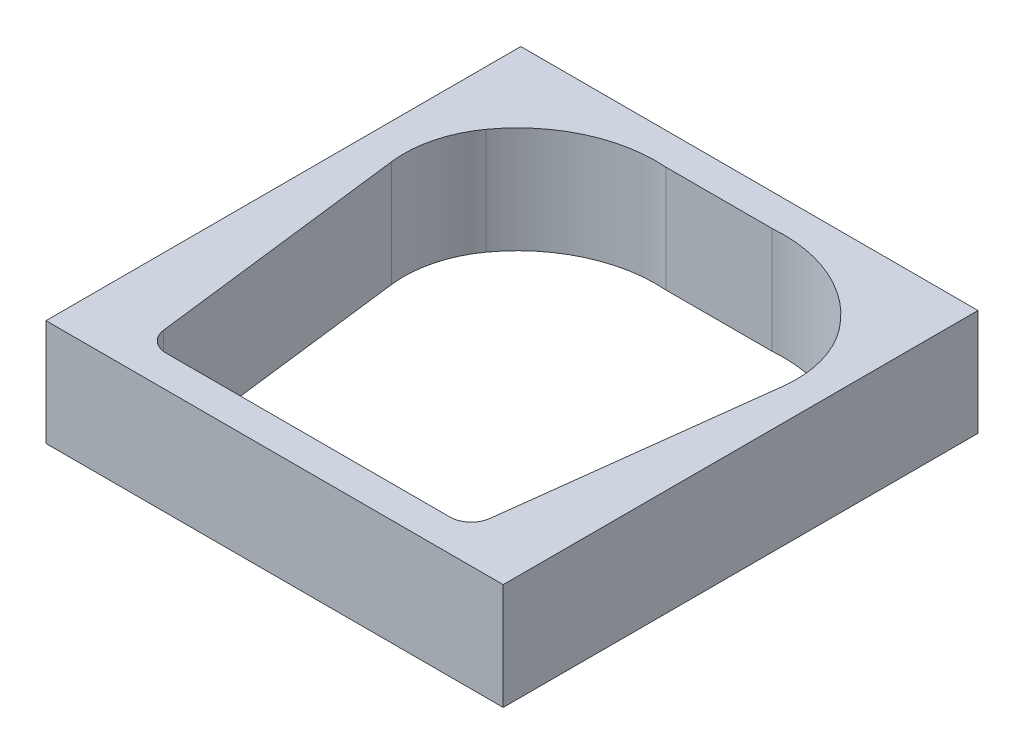
SolidWorks part; units mm, degrees
ref_plane "Front Plane" through (0, 0, 0) normal (0, 0, 1) x (1, 0, 0)
ref_plane "Top Plane" through (0, 0, 0) normal (0, 1, 0) x (1, 0, 0)
ref_plane "Right Plane" through (0, 0, 0) normal (1, 0, 0) x (0, 0, -1)
sketch "Sketch1" plane through (0, 0, 0) normal (0, 1, 0) x (1, 0, 0)
  line L1 (13.6302, 10) -> (23.6302, 10)
  line L3 (0.2982, -2.4286) -> (3.2992, -26.87)
  line L4 (5.2843, -28.6263) -> (31.976, -28.6263)
  line L5 (36.9706, -2.3598) -> (33.9611, -26.87)
  arc A0 (2.1102, 4.6358) -> (13.6302, 10) centre (12.6577, -2.9636) cw
  arc A1 (34.9994, 4.9193) -> (23.6302, 10) centre (24.6588, -2.9592) ccw
  arc A2 (36.9706, -2.3598) -> (34.9994, 4.9193) centre (27.0451, -1.1411) ccw
  arc A3 (0.2982, -2.4286) -> (2.1102, 4.6358) centre (10.2237, -1.2099) cw
  arc A4 (31.976, -28.6263) -> (33.9611, -26.87) centre (31.976, -26.6263) ccw
  arc A5 (3.2992, -26.87) -> (5.2843, -28.6263) centre (5.2843, -26.6263) ccw
  point P5 (2.911, -28.8286)
  point P10 (33.8055, -28.5469)
  point P11 (5.3794, 5.7623)
  point P12 (4.3868, 2.3991)
  point P13 (6.5004, 7.599)
  point P14 (0, 0)
  point P15 (4.5124, 4.9762)
  point P16 (0, 0)
  point P17 (0, 0)
  point P18 (0, 0)
  point P19 (10.4858, 0)
  point P20 (18.6302, 10)
  point P21 (18.6302, -28.6263)
  point P24 (37.2797, 0.1575)
  point P27 (0, 0)
  point P30 (33.7455, -28.6263)
  dimension "D3" = 10
  dimension "D7" = 13
  dimension "D8" = 10
  dimension "D9" = 2
  dimension "D1" = 37.28
  dimension "D2" = 29
  dimension "D4" = 10
  dimension "D5" = 83
  dimension "D6" = 83
extrude "Boss-Extrude1" add sketch "Sketch1" along normal blind 2133.6
sketch "Sketch2" plane through (0, 0, 0) normal (0, 1, 0) x (1, 0, 0)
  line L0 (5.2843, -28.6263) -> (31.976, -28.6263) construction
  line L1 (-3, -31.6263) -> (39.9706, -31.6263)
  line L2 (-3, -31.6263) -> (-3, 13)
  line L3 (-3, 13) -> (39.9706, 13)
  line L4 (39.9706, -31.6263) -> (39.9706, 13)
  line L5 (23.6302, 10) -> (13.6302, 10) construction
  dimension "D1" = 3
  dimension "D2" = 3
  dimension "D3" = 3
  dimension "D4" = 3
extrude "Boss-Extrude2" add sketch "Sketch2" along normal blind 10
sketch "Sketch3" plane through (0, 0, 0) normal (0, 1, 0) x (1, 0, 0)
  line L8 (0.2982, -2.4286) -> (3.2992, -26.87)
  line L9 (5.2843, -28.6263) -> (31.976, -28.6263)
  line L10 (33.9611, -26.87) -> (36.9706, -2.3598)
  line L11 (23.6302, 10) -> (13.6302, 10)
  line L12 (0.2982, -2.4286) -> (3.2992, -26.87)
  line L13 (5.2843, -28.6263) -> (31.976, -28.6263)
  line L14 (33.9611, -26.87) -> (36.9706, -2.3598)
  line L15 (23.6302, 10) -> (13.6302, 10)
  arc A12 (13.6302, 10) -> (2.1102, 4.6358) centre (12.6577, -2.9636) ccw
  arc A13 (2.1102, 4.6358) -> (0.2982, -2.4286) centre (10.2237, -1.2099) ccw
  arc A14 (3.2992, -26.87) -> (5.2843, -28.6263) centre (5.2843, -26.6263) ccw
  arc A15 (31.976, -28.6263) -> (33.9611, -26.87) centre (31.976, -26.6263) ccw
  arc A16 (36.9706, -2.3598) -> (34.9994, 4.9193) centre (27.0451, -1.1411) ccw
  arc A17 (34.9994, 4.9193) -> (23.6302, 10) centre (24.6588, -2.9592) ccw
  arc A18 (13.6302, 10) -> (2.1102, 4.6358) centre (12.6577, -2.9636) ccw
  arc A19 (2.1102, 4.6358) -> (0.2982, -2.4286) centre (10.2237, -1.2099) ccw
  arc A20 (3.2992, -26.87) -> (5.2843, -28.6263) centre (5.2843, -26.6263) ccw
  arc A21 (31.976, -28.6263) -> (33.9611, -26.87) centre (31.976, -26.6263) ccw
  arc A22 (36.9706, -2.3598) -> (34.9994, 4.9193) centre (27.0451, -1.1411) ccw
  arc A23 (34.9994, 4.9193) -> (23.6302, 10) centre (24.6588, -2.9592) ccw
  dimension "D1" = 0
extrude "Cut-Extrude1" cut sketch "Sketch3" against normal through all and the other way through all
